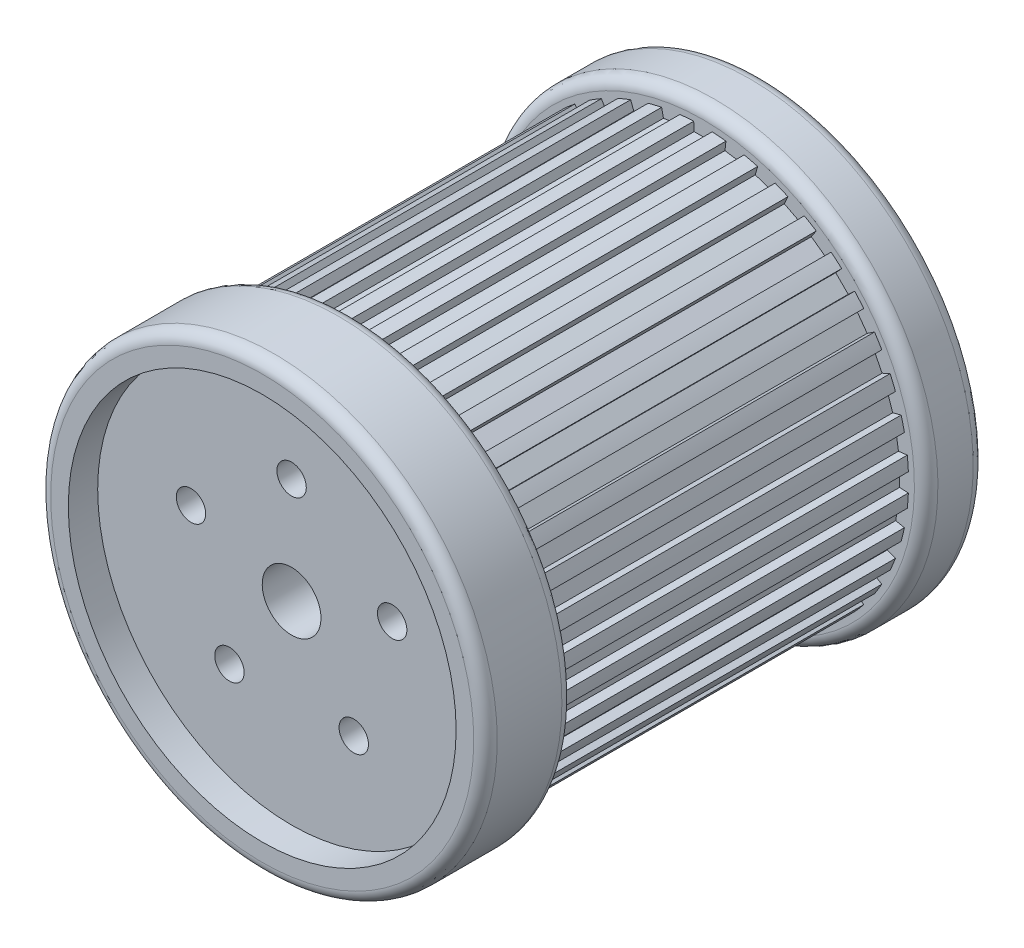
SolidWorks part; units mm, degrees
ref_plane "Front Plane" through (0, 0, 0) normal (0, 0, 1) x (1, 0, 0)
ref_plane "Top Plane" through (0, 0, 0) normal (0, 1, 0) x (1, 0, 0)
ref_plane "Right Plane" through (0, 0, 0) normal (1, 0, 0) x (0, 0, -1)
sketch "Sketch1" plane through (0, 0, 0) normal (1, 0, 0) x (0, 0, -1)
  line L0 (-17.5, 0) -> (-27.5, 0)
  line L1 (-27.5, 0) -> (-27.5, -35)
  line L2 (-27.5, -35) -> (52.5, -35)
  line L3 (52.5, -35) -> (52.5, -25)
  line L4 (52.5, -25) -> (-17.5, -25)
  line L5 (-17.5, -25) -> (-17.5, 0)
  dimension "D1" = 25
  dimension "D2" = 10
  dimension "D3" = 10
  dimension "D4" = 17.5
  dimension "D5" = 80
revolve "Revolve1" add sketch "Sketch1" angle 360 about L0
sketch "Sketch2" plane through (0, 0, 17.5) normal (0, 0, -1) x (-1, 0, 0)
  circle A0 centre (0, 0) radius 18 construction
  circle A1 centre (0, 0) radius 5
  circle A2 centre (0, 18) radius 2.5
  circle A3 centre (17.119, 5.5623) radius 2.5
  circle A4 centre (10.5801, -14.5623) radius 2.5
  circle A5 centre (-10.5801, -14.5623) radius 2.5
  circle A6 centre (-17.119, 5.5623) radius 2.5
  point P16 (0, 0)
  dimension "D1" = 36
  dimension "D2" = 10
  dimension "D3" = 5
  dimension "D4" = 5
extrude "Cut-Extrude2" cut sketch "Sketch2" against normal through all
sketch "Sketch3" plane through (0, 0, -52.5) normal (0, 0, -1) x (-1, 0, 0)
  line L0 (-1.5, 33.4649) -> (1.5, 33.4649)
  line L1 (1.5, 33.4649) -> (1.5672, 34.9649)
  line L2 (-1.5, 33.4649) -> (-1.5672, 34.9649)
  circle A0 centre (0, 0) radius 35 construction
  arc A1 (1.5672, 34.9649) -> (-1.5672, 34.9649) centre (0, 0) ccw
  point P2 (0, 33.4649)
  dimension "D1" = 3
  dimension "D2" = 1.5
extrude "Cut-Extrude3" cut sketch "Sketch3" against normal blind 70
sketch "Sketch4" plane through (0, 0, 27.5) normal (0, 0, 1) x (1, 0, 0)
  circle A0 centre (0, 0) radius 38
  circle A1 centre (0, 0) radius 35
  circle A2 centre (0, 0) radius 35
  dimension "D1" = 0
  dimension "D2" = 3
extrude "Boss-Extrude1" add sketch "Sketch4" against normal up to surface (10 mm away) up to face at (0, 34.2237, 17.5)
pattern_circular "CirPattern1" count 40 over 360 about axis through (0, 0, 0) along (0, 0, 1) of "Cut-Extrude3"
sketch "Sketch5" plane through (0, 0, 27.5) normal (0, 0, 1) x (1, 0, 0)
  circle A2 centre (0, 0) radius 38 construction
  circle A4 centre (0, 0) radius 38
  circle A5 centre (0, 0) radius 33
  circle A6 centre (0, 0) radius 33
  dimension "D2" = 5
extrude "Boss-Extrude2" add sketch "Sketch5" along normal blind 5 contours A4 | A6
sketch "Sketch6" plane through (0, 0, -52.5) normal (0, 0, -1) x (-1, 0, 0)
  circle A0 centre (0, 0) radius 32
  circle A1 centre (0, 0) radius 38 construction
  circle A2 centre (0, 0) radius 38
  dimension "D1" = 64
extrude "Boss-Extrude3" add sketch "Sketch6" against normal blind 10
fillet "Fillet1" radius 3 1 edges at (0, 25, -52.5)
fillet "Fillet2" radius 2 4 edges at (38, 0, 32.5) (0, 38, 17.5) (0, 38, -42.5) (0, 38, -52.5)
